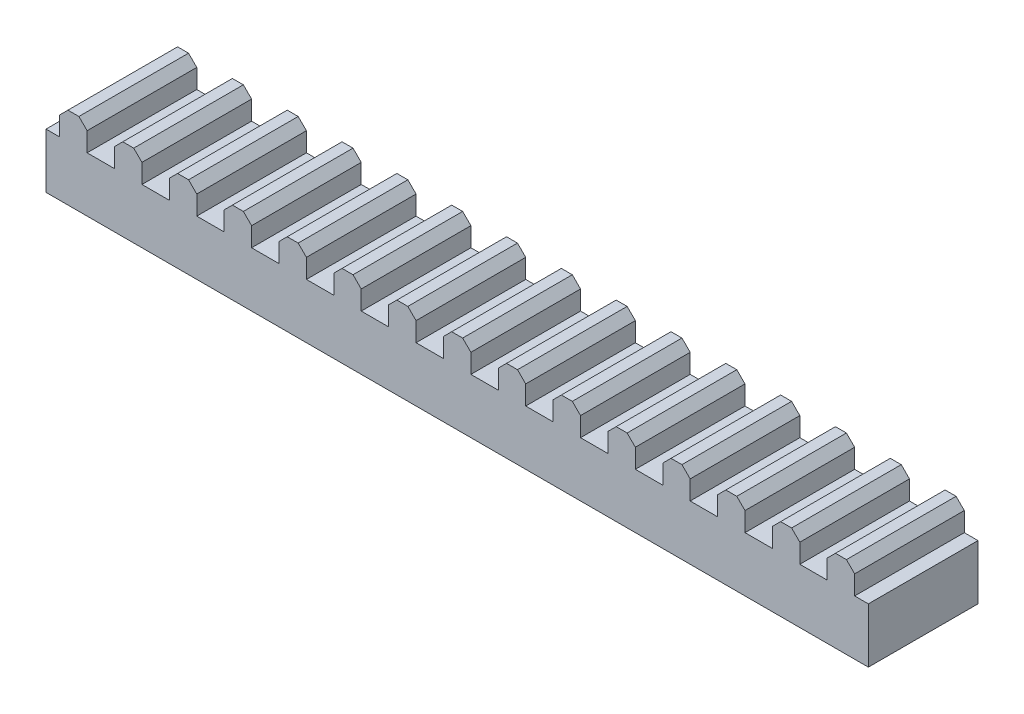
SolidWorks part; units mm, degrees
ref_plane "Front Plane" through (0, 0, 0) normal (0, 0, 1) x (1, 0, 0)
ref_plane "Top Plane" through (0, 0, 0) normal (0, 1, 0) x (1, 0, 0)
ref_plane "Right Plane" through (0, 0, 0) normal (1, 0, 0) x (0, 0, -1)
sketch "Sketch1" plane through (0, 0, 0) normal (0, 0, 1) x (1, 0, 0)
  line L1 (381, -25.4) -> (-381, -25.4)
  line L2 (381, -25.4) -> (381, 25.4)
  line L3 (381, 25.4) -> (-381, 25.4)
  line L4 (-381, -25.4) -> (-381, 25.4)
  line L5 (381, -25.4) -> (-381, 25.4) construction
  line L6 (381, 25.4) -> (-381, -25.4) construction
  point P0 (0, 0)
  dimension "D1" = 762
  dimension "D2" = 50.8
extrude "Boss-Extrude1" add sketch "Sketch1" along normal mid plane 101.6
sketch "Sketch2" plane through (0, 0, 50.8) normal (0, 0, 1) x (1, 0, 0)
  line L0 (0, 0) -> (0, 50.7636) construction
  line L1 (-241.3, 25.4) -> (-266.7, 25.4)
  line L2 (381, 25.4) -> (-381, 25.4) construction
  line L3 (368.3, 25.4) -> (342.9, 25.4)
  line L4 (12.7, 25.4) -> (12.7, 50.7636)
  line L5 (-12.7, 50.7636) -> (12.7, 50.7636)
  line L6 (-12.7, 25.4) -> (-12.7, 50.7636)
  line L7 (38.1, 50.7636) -> (63.5, 50.7636)
  line L8 (38.1, 25.4) -> (38.1, 50.7636)
  line L9 (63.5, 25.4) -> (63.5, 50.7636)
  line L10 (88.9, 50.7636) -> (114.3, 50.7636)
  line L11 (88.9, 25.4) -> (88.9, 50.7636)
  line L12 (114.3, 25.4) -> (114.3, 50.7636)
  line L13 (139.7, 50.7636) -> (165.1, 50.7636)
  line L14 (139.7, 25.4) -> (139.7, 50.7636)
  line L15 (165.1, 25.4) -> (165.1, 50.7636)
  line L16 (190.5, 50.7636) -> (215.9, 50.7636)
  line L17 (190.5, 25.4) -> (190.5, 50.7636)
  line L18 (215.9, 25.4) -> (215.9, 50.7636)
  line L19 (241.3, 50.7636) -> (266.7, 50.7636)
  line L20 (241.3, 25.4) -> (241.3, 50.7636)
  line L21 (266.7, 25.4) -> (266.7, 50.7636)
  line L22 (292.1, 50.7636) -> (317.5, 50.7636)
  line L23 (292.1, 25.4) -> (292.1, 50.7636)
  line L24 (317.5, 25.4) -> (317.5, 50.7636)
  line L25 (342.9, 50.7636) -> (368.3, 50.7636)
  line L26 (342.9, 25.4) -> (342.9, 50.7636)
  line L27 (368.3, 25.4) -> (368.3, 50.7636)
  line L28 (-63.5, 50.7636) -> (-38.1, 50.7636)
  line L29 (-63.5, 25.4) -> (-63.5, 50.7636)
  line L30 (-38.1, 25.4) -> (-38.1, 50.7636)
  line L31 (-114.3, 50.7636) -> (-88.9, 50.7636)
  line L32 (-114.3, 25.4) -> (-114.3, 50.7636)
  line L33 (-88.9, 25.4) -> (-88.9, 50.7636)
  line L34 (-165.1, 50.7636) -> (-139.7, 50.7636)
  line L35 (-165.1, 25.4) -> (-165.1, 50.7636)
  line L36 (-139.7, 25.4) -> (-139.7, 50.7636)
  line L37 (-215.9, 50.7636) -> (-190.5, 50.7636)
  line L38 (-215.9, 25.4) -> (-215.9, 50.7636)
  line L39 (-190.5, 25.4) -> (-190.5, 50.7636)
  line L40 (-266.7, 50.7636) -> (-241.3, 50.7636)
  line L41 (-266.7, 25.4) -> (-266.7, 50.7636)
  line L42 (-241.3, 25.4) -> (-241.3, 50.7636)
  line L43 (-317.5, 50.7636) -> (-292.1, 50.7636)
  line L44 (-317.5, 25.4) -> (-317.5, 50.7636)
  line L45 (-292.1, 25.4) -> (-292.1, 50.7636)
  line L46 (-368.3, 50.7636) -> (-342.9, 50.7636)
  line L47 (-368.3, 25.4) -> (-368.3, 50.7636)
  line L48 (-342.9, 25.4) -> (-342.9, 50.7636)
  line L49 (-292.1, 25.4) -> (-317.5, 25.4)
  line L50 (-342.9, 25.4) -> (-368.3, 25.4)
  line L51 (-190.5, 25.4) -> (-215.9, 25.4)
  line L52 (-139.7, 25.4) -> (-165.1, 25.4)
  line L53 (-88.9, 25.4) -> (-114.3, 25.4)
  line L54 (-38.1, 25.4) -> (-63.5, 25.4)
  line L55 (12.7, 25.4) -> (-12.7, 25.4)
  line L56 (63.5, 25.4) -> (38.1, 25.4)
  line L57 (114.3, 25.4) -> (88.9, 25.4)
  line L58 (165.1, 25.4) -> (139.7, 25.4)
  line L59 (215.9, 25.4) -> (190.5, 25.4)
  line L60 (266.7, 25.4) -> (241.3, 25.4)
  line L61 (317.5, 25.4) -> (292.1, 25.4)
  dimension "D1" = 12.7
  dimension "D2" = 8
  dimension "D3" = 8
extrude "Boss-Extrude2" add sketch "Sketch2" against normal through all
chamfer "Chamfer1" distance 7.62 angle 45 30 edges at (-368.3, 50.7636, 0) (-317.5, 50.7636, 0) (-266.7, 50.7636, 0) (-215.9, 50.7636, 0) (-165.1, 50.7636, 0) (-114.3, 50.7636, 0) (-63.5, 50.7636, 0) (-12.7, 50.7636, 0) (38.1, 50.7636, 0) (88.9, 50.7636, 0) (139.7, 50.7636, 0) (190.5, 50.7636, 0) (241.3, 50.7636, 0) (292.1, 50.7636, 0) (342.9, 50.7636, 0) (368.3, 50.7636, 0) (317.5, 50.7636, 0) (266.7, 50.7636, 0) (215.9, 50.7636, 0) (165.1, 50.7636, 0) (114.3, 50.7636, 0) (63.5, 50.7636, 0) (12.7, 50.7636, 0) (-38.1, 50.7636, 0) (-88.9, 50.7636, 0) (-139.7, 50.7636, 0) (-190.5, 50.7636, 0) (-241.3, 50.7636, 0) (-342.9, 50.7636, 0) (-292.1, 50.7636, 0)
